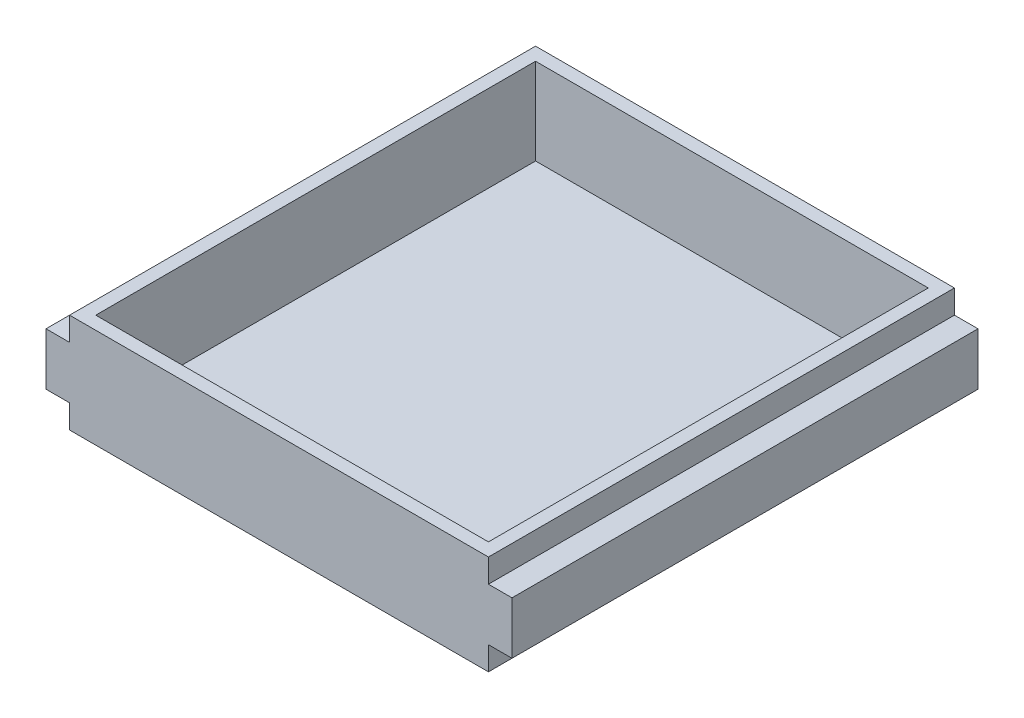
SolidWorks part; units mm, degrees
ref_plane "Front Plane" through (0, 0, 0) normal (0, 0, 1) x (1, 0, 0)
ref_plane "Top Plane" through (0, 0, 0) normal (0, 1, 0) x (1, 0, 0)
ref_plane "Right Plane" through (0, 0, 0) normal (1, 0, 0) x (0, 0, -1)
sketch "Sketch1" plane through (0, 0, 0) normal (0, 0, 1) x (1, 0, 0)
  line L0 (89, 98.84) -> (89, -52.52) construction
  line L1 (169, -9) -> (9, -9)
  line L2 (9, -9) -> (9, 0)
  line L3 (9, 0) -> (0, 0)
  line L4 (0, 0) -> (0, 20)
  line L5 (0, 20) -> (9, 20)
  line L6 (9, 20) -> (9, 29)
  line L7 (9, 29) -> (169, 29)
  line L8 (169, -9) -> (169, 0)
  line L9 (169, 0) -> (178, 0)
  line L10 (178, 0) -> (178, 20)
  line L11 (178, 20) -> (169, 20)
  line L12 (169, 20) -> (169, 29)
  point P12 (89, -9)
  point P17 (89, 29)
  dimension "D1" = 20
  dimension "D2" = 9
  dimension "D3" = 9
  dimension "D4" = 9
  dimension "D5" = 9
  dimension "D6" = 80
extrude "Boss-Extrude1" add sketch "Sketch1" against normal blind 178
sketch "Sketch2" plane through (0, 29, 0) normal (0, 1, 0) x (1, 0, 0)
  line L0 (9, 178) -> (9, 0) construction
  line L1 (164, 173) -> (14, 173)
  line L2 (164, 173) -> (164, 5)
  line L3 (164, 5) -> (14, 5)
  line L4 (14, 173) -> (14, 5)
  line L5 (169, 178) -> (9, 178) construction
  dimension "D1" = 150
  dimension "D2" = 168
  dimension "D3" = 5
  dimension "D4" = 5
extrude "Cut-Extrude1" cut sketch "Sketch2" against normal blind 33
